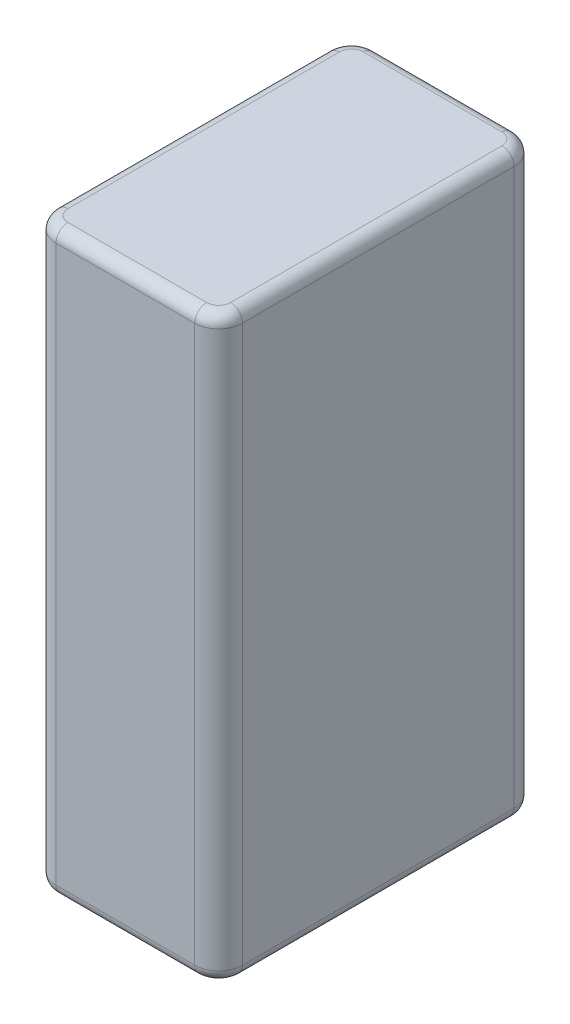
SolidWorks part; units mm, degrees
ref_plane "Front Plane" through (0, 0, 0) normal (0, 0, 1) x (1, 0, 0)
ref_plane "Top Plane" through (0, 0, 0) normal (0, 1, 0) x (1, 0, 0)
ref_plane "Right Plane" through (0, 0, 0) normal (1, 0, 0) x (0, 0, -1)
sketch "Sketch1" plane through (0, 0, 0) normal (0, 1, 0) x (1, 0, 0)
  line L0 (-7.8, -13.35) -> (7.8, 13.35) construction
  line L1 (-7.8, 13.35) -> (7.8, 13.35)
  line L2 (-7.8, 13.35) -> (-7.8, -13.35)
  line L3 (-7.8, -13.35) -> (7.8, -13.35)
  line L4 (7.8, 13.35) -> (7.8, -13.35)
  point P4 (0, 0)
  dimension "D1" = 26.7
  dimension "D2" = 15.6
extrude "Extrude1" add sketch "Sketch1" along normal blind 48.5
fillet "Fillet1" radius 2 4 edges at (-7.8, 24.25, 13.35) (-7.8, 24.25, -13.35) (7.8, 24.25, -13.35) (7.8, 24.25, 13.35)
fillet "Fillet2" radius 1 16 edges at (-7.2142, 48.5, -12.7642) (0, 48.5, -13.35) (7.2142, 48.5, -12.7642) (7.8, 48.5, 0) (7.2142, 48.5, 12.7642) (0, 48.5, 13.35) (-7.2142, 48.5, 12.7642) (-7.2142, 0, -12.7642) (0, 0, -13.35) (7.2142, 0, -12.7642) (7.8, 0, 0) (7.2142, 0, 12.7642) (0, 0, 13.35) (-7.2142, 0, 12.7642) (-7.8, 48.5, 0) (-7.8, 0, 0)
